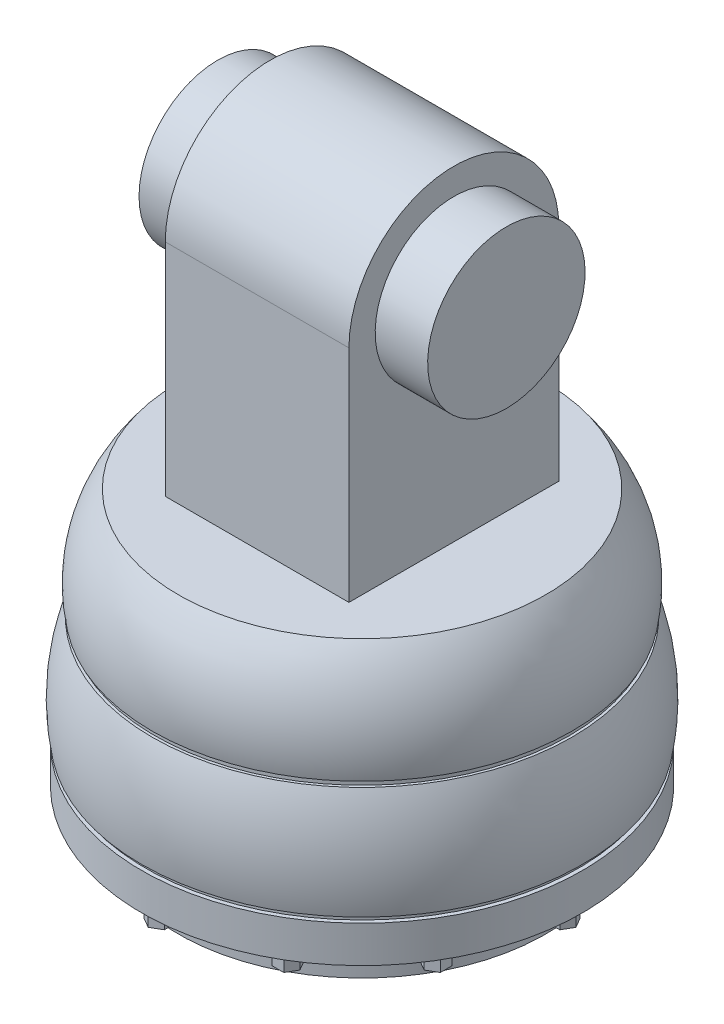
SolidWorks part; units mm, degrees
ref_plane "Front Plane" through (0, 0, 0) normal (0, 0, 1) x (1, 0, 0)
ref_plane "Top Plane" through (0, 0, 0) normal (0, 1, 0) x (1, 0, 0)
ref_plane "Right Plane" through (0, 0, 0) normal (1, 0, 0) x (0, 0, -1)
sketch "Sketch1" plane through (0, 0, 0) normal (0, 0, 1) x (1, 0, 0)
  line L0 (-35, 0) -> (0, 0)
  line L1 (0, 0) -> (0, -20)
  line L2 (0, -20) -> (-40, -20)
  arc A0 (-35, 0) -> (-40, -20) centre (-15.404, -15.524) ccw
  dimension "D4" = 25
  dimension "D1" = 35
  dimension "D2" = 20
  dimension "D3" = 40
revolve "Revolve1" add sketch "Sketch1" angle 360 about L1
sketch "Sketch2" plane through (0, -20, 0) normal (0, -1, 0) x (1, 0, 0)
  circle A0 centre (0, 0) radius 39.5
  dimension "D1" = 79
extrude "Boss-Extrude1" add sketch "Sketch2" along normal blind 1
sketch "Sketch3" plane through (0, 0, 0) normal (1, 0, 0) x (0, 0, -1)
  line L0 (0, -21) -> (-40, -21)
  line L1 (-39.5, -21) -> (39.5, -21) construction
  line L2 (0, -21) -> (0, -41)
  line L3 (0, -41) -> (-42, -41)
  arc A0 (-40, -21) -> (-42, -41) centre (-5.5677, -34.5432) ccw
  dimension "D4" = 37
  dimension "D1" = 40
  dimension "D2" = 20
  dimension "D3" = 42
revolve "Revolve2" add sketch "Sketch3" angle 360 about L2
sketch "Sketch4" plane through (0, -41, 0) normal (0, -1, 0) x (1, 0, 0)
  circle A0 centre (0, 0) radius 41.25
  dimension "D1" = 82.5
extrude "Boss-Extrude2" add sketch "Sketch4" along normal blind 1
sketch "Sketch5" plane through (0, -42, 0) normal (0, -1, 0) x (1, 0, 0)
  circle A0 centre (0, 0) radius 42
  dimension "D1" = 84
extrude "Boss-Extrude3" add sketch "Sketch5" along normal blind 7
sketch "Sketch6" plane through (0, -49, 0) normal (0, -1, 0) x (1, 0, 0)
  circle A0 centre (0, 0) radius 35
  dimension "D1" = 70
extrude "Boss-Extrude4" add sketch "Sketch6" along normal blind 7
sketch "Sketch7" plane through (0, -49, 0) normal (0, -1, 0) x (1, 0, 0)
  line L0 (35, 0) -> (42, 0) construction
  line L1 (39.0476, 0.9486) -> (37.9524, 0.9486)
  line L2 (40.75, 0) -> (39.625, 1.9486)
  line L3 (39.625, 1.9486) -> (37.375, 1.9486)
  line L4 (37.375, 1.9486) -> (36.25, 0)
  line L5 (36.25, 0) -> (37.375, -1.9486)
  line L6 (37.375, -1.9486) -> (39.625, -1.9486)
  line L7 (39.625, -1.9486) -> (40.75, 0)
  line L8 (37.9524, 0.9486) -> (37.4047, 0)
  line L9 (37.4047, 0) -> (37.9524, -0.9486)
  line L10 (37.9524, -0.9486) -> (39.0476, -0.9486)
  line L11 (39.0476, -0.9486) -> (39.5953, 0)
  line L12 (39.5953, 0) -> (39.0476, 0.9486)
  circle A0 centre (0, 0) radius 35 construction
  circle A1 centre (0, 0) radius 35 construction
  circle A2 centre (0, 0) radius 42 construction
  circle A3 centre (38.5, 0) radius 1.9486 construction
  dimension "D1" = 4.5
  dimension "D2" = 1
extrude "Boss-Extrude5" add sketch "Sketch7" along normal blind 3
pattern_circular "CirPattern1" count 12 over 360 about axis through (0, 0, 0) along (0, 1, 0) of "Boss-Extrude5"
sketch "Sketch8" plane through (0, -56, 0) normal (0, -1, 0) x (1, 0, 0)
  circle A0 centre (0, 0) radius 15
  dimension "D1" = 30
extrude "Boss-Extrude6" add sketch "Sketch8" along normal blind 10
sketch "Sketch9" plane through (0, 0, 0) normal (0, 1, 0) x (1, 0, 0)
  line L1 (-17.5, -20) -> (17.5, -20)
  line L2 (-17.5, -20) -> (-17.5, 20)
  line L3 (-17.5, 20) -> (17.5, 20)
  line L4 (17.5, -20) -> (17.5, 20)
  line L5 (-17.5, -20) -> (17.5, 20) construction
  line L6 (-17.5, 20) -> (17.5, -20) construction
  point P0 (0, 0)
  dimension "D1" = 35
  dimension "D2" = 40
extrude "Boss-Extrude7" add sketch "Sketch9" along normal blind 42
sketch "Sketch10" plane through (-17.5, 0, 0) normal (-1, 0, 0) x (0, 0, 1)
  line L0 (-20, 42) -> (20, 42) construction
  line L1 (-20, 42) -> (20, 42)
  arc A0 (20, 42) -> (-20, 42) centre (0, 42) ccw
extrude "Boss-Extrude8" add sketch "Sketch10" against normal blind 35
sketch "Sketch11" plane through (-17.5, 0, 0) normal (-1, 0, 0) x (0, 0, 1)
  circle A0 centre (0, 42) radius 15
  dimension "D1" = 30
extrude "Boss-Extrude9" add sketch "Sketch11" along normal blind 10
mirror "Mirror1" about plane through (0, 0, 0) normal (1, 0, 0) of "Boss-Extrude9"
